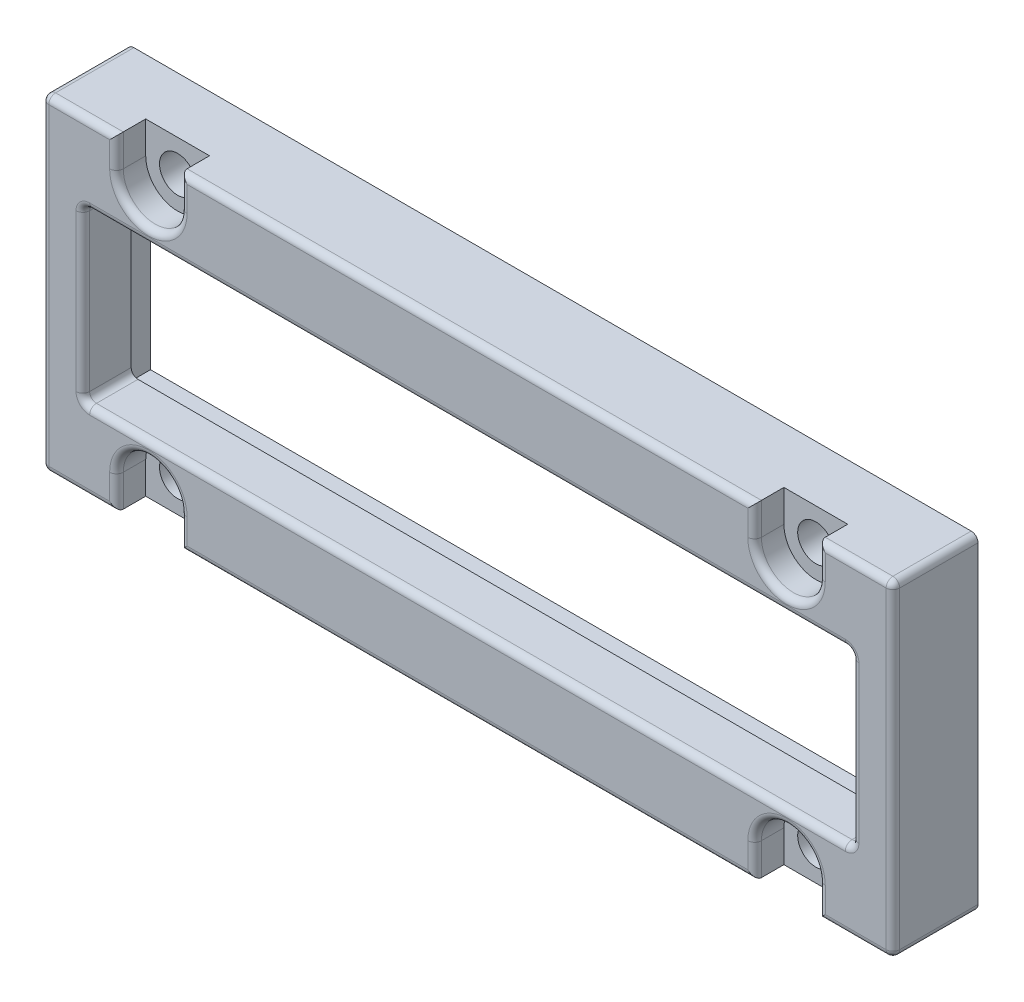
SolidWorks part; units mm, degrees
material "Nylon 101"
ref_plane "Front Plane" through (0, 0, 0) normal (0, 0, 1) x (1, 0, 0)
ref_plane "Top Plane" through (0, 0, 0) normal (0, 1, 0) x (1, 0, 0)
ref_plane "Right Plane" through (0, 0, 0) normal (1, 0, 0) x (0, 0, -1)
sketch "Sketch1" plane through (0, 0, 0) normal (0, 0, 1) x (1, 0, 0)
  line L1 (168.9878, -189.8186) -> (105.4878, -189.8186)
  line L2 (168.9878, -189.8186) -> (168.9878, -165.4346)
  line L3 (168.9878, -165.4346) -> (105.4878, -165.4346)
  line L4 (105.4878, -189.8186) -> (105.4878, -165.4346)
  line L5 (168.9878, -189.8186) -> (105.4878, -165.4346) construction
  line L6 (168.9878, -165.4346) -> (105.4878, -189.8186) construction
  point P4 (137.2378, -177.6266)
extrude "Boss-Extrude1" add sketch "Sketch1" along normal blind 6.35
hole_wizard "CBORE for #2 Socket Head Cap Screw1" positions "Sketch3" profile "Sketch2" counterbore size "#2" standard "ANSI Inch" end condition through all
sketch "Sketch3" plane through (0, 0, 6.35) normal (0, 0, 1) x (1, 0, 0)
  line L0 (163.0823, -187.7866) -> (161.0503, -187.7866) construction
  line L2 (161.0503, -189.8186) -> (161.0503, -165.4346) construction
  line L3 (105.4878, -189.8186) -> (168.9878, -189.8186) construction
  line L4 (168.9878, -165.4346) -> (105.4878, -165.4346) construction
  line L5 (161.0503, -177.6266) -> (168.9878, -177.6266) construction
  line L6 (168.9878, -189.8186) -> (168.9878, -165.4346) construction
  line L8 (137.2378, -189.8186) -> (137.2378, -165.4346) construction
  point P14 (161.0503, -187.431)
  point P26 (113.4253, -187.431)
  point P28 (161.0503, -167.8222)
  point P29 (113.4253, -167.8222)
  dimension "D1" = 2.3876
sketch "Sketch2" plane through (161.0503, -187.431, 6.35) normal (1, 0, 0) x (0, -1, 0)
  line L0 (0, 0) -> (0, 6.35)
  line L1 (0, 6.35) -> (1.3525, 6.35)
  line L3 (1.3525, 6.35) -> (1.3526, 2.1844)
  line L4 (1.3526, 2.1844) -> (2.3812, 2.1844)
  line L5 (2.3812, 2.1844) -> (2.3812, 0)
  line L7 (2.3812, 0) -> (0, 0)
  line L11 (0, -6.35) -> (0, 107.95) construction
  dimension "Thru Hole Dia." = 2.7051
  dimension "Thru Hole Depth" = 6.35
  dimension "C'Bore Dia." = 4.7625
  dimension "C'Bore Depth" = 2.1844
sketch "Sketch4" plane through (0, 0, 6.35) normal (0, 0, 1) x (1, 0, 0)
  line L1 (165.9398, -183.9766) -> (108.5358, -183.9766)
  line L2 (165.9398, -183.9766) -> (165.9398, -171.2766)
  line L3 (165.9398, -171.2766) -> (108.5358, -171.2766)
  line L4 (108.5358, -183.9766) -> (108.5358, -171.2766)
  line L5 (165.9398, -183.9766) -> (108.5358, -171.2766) construction
  line L6 (165.9398, -171.2766) -> (108.5358, -183.9766) construction
  point P4 (137.2378, -177.6266)
extrude "Cut-Extrude1" cut sketch "Sketch4" against normal through all
sketch "Sketch5" plane through (0, 0, 6.35) normal (0, 0, 1) x (1, 0, 0)
  line L0 (168.9878, -165.4346) -> (105.4878, -165.4346) construction
  line L1 (111.0441, -167.8222) -> (115.8066, -167.8222)
  line L2 (111.0441, -167.8222) -> (111.0441, -165.4346)
  line L3 (111.0441, -165.4346) -> (115.8066, -165.4346)
  line L4 (115.8066, -167.8222) -> (115.8066, -165.4346)
  line L5 (111.0441, -167.8222) -> (115.8066, -165.4346) construction
  line L6 (111.0441, -165.4346) -> (115.8066, -167.8222) construction
  line L7 (137.2378, -165.4346) -> (137.2378, -177.6266) construction
  line L8 (137.2378, -177.6266) -> (105.4878, -177.6266) construction
  line L9 (105.4878, -165.4346) -> (105.4878, -189.8186) construction
  line L10 (163.4316, -167.8222) -> (163.4316, -165.4346)
  line L11 (163.4316, -165.4346) -> (158.6691, -165.4346)
  line L12 (158.6691, -167.8222) -> (158.6691, -165.4346)
  line L13 (163.4316, -167.8222) -> (158.6691, -167.8222)
  line L14 (111.0441, -189.8186) -> (115.8066, -189.8186)
  line L15 (111.0441, -187.431) -> (111.0441, -189.8186)
  line L16 (111.0441, -187.431) -> (115.8066, -187.431)
  line L17 (115.8066, -187.431) -> (115.8066, -189.8186)
  line L18 (163.4316, -187.431) -> (158.6691, -187.431)
  line L19 (158.6691, -187.431) -> (158.6691, -189.8186)
  line L20 (163.4316, -189.8186) -> (158.6691, -189.8186)
  line L21 (163.4316, -187.431) -> (163.4316, -189.8186)
  circle A0 centre (113.4253, -167.8222) radius 2.3813 construction
  point P0 (113.4253, -167.8222)
  point P6 (113.4253, -166.6284)
  point P11 (113.4253, -167.8222)
extrude "Cut-Extrude2" cut sketch "Sketch5" against normal up to surface (2.1844 mm away) up to face at (114.7779, -167.8222, 4.1656)
sketch "Sketch7" plane through (0, 0, 0) normal (0, 0, -1) x (-1, 0, 0)
  line L0 (-163.4316, -167.8222) -> (-163.4316, -165.4346) construction
  line L1 (-158.6691, -165.4346) -> (-158.6691, -167.8222) construction
  line L2 (-115.8066, -167.8222) -> (-115.8066, -165.4346) construction
  line L3 (-111.0441, -165.4346) -> (-111.0441, -167.8222) construction
  line L4 (-111.0441, -187.431) -> (-111.0441, -189.8186) construction
  line L5 (-115.8066, -189.8186) -> (-115.8066, -187.431) construction
  line L6 (-158.6691, -187.431) -> (-158.6691, -189.8186) construction
  line L7 (-163.4316, -189.8186) -> (-163.4316, -187.431) construction
  line L8 (-163.4316, -167.8222) -> (-163.4316, -166.7046)
  line L9 (-158.6691, -166.7046) -> (-158.6691, -167.8222)
  line L10 (-115.8066, -167.8222) -> (-115.8066, -166.7046)
  line L11 (-111.0441, -166.7046) -> (-111.0441, -167.8222)
  line L12 (-111.0441, -187.431) -> (-111.0441, -188.5486)
  line L13 (-115.8066, -188.5486) -> (-115.8066, -187.431)
  line L14 (-158.6691, -187.431) -> (-158.6691, -188.5486)
  line L15 (-163.4316, -188.5486) -> (-163.4316, -187.431)
  line L20 (-168.9878, -165.4346) -> (-168.9878, -189.8186)
  line L21 (-168.9878, -189.8186) -> (-105.4878, -189.8186)
  line L22 (-105.4878, -189.8186) -> (-105.4878, -165.4346)
  line L23 (-105.4878, -165.4346) -> (-168.9878, -165.4346)
  line L24 (-168.9878, -165.4346) -> (-168.9878, -189.8186) construction
  line L25 (-168.9878, -189.8186) -> (-105.4878, -189.8186) construction
  line L26 (-105.4878, -189.8186) -> (-105.4878, -165.4346) construction
  line L27 (-105.4878, -165.4346) -> (-168.9878, -165.4346) construction
  line L28 (-106.7578, -166.7046) -> (-111.0441, -166.7046)
  line L29 (-167.7178, -166.7046) -> (-167.7178, -188.5486)
  line L30 (-167.7178, -188.5486) -> (-163.4316, -188.5486)
  line L31 (-106.7578, -188.5486) -> (-106.7578, -166.7046)
  line L32 (-165.9398, -183.9766) -> (-108.5358, -183.9766)
  line L33 (-165.9398, -171.2766) -> (-165.9398, -183.9766)
  line L34 (-108.5358, -171.2766) -> (-165.9398, -171.2766)
  line L35 (-108.5358, -183.9766) -> (-108.5358, -171.2766)
  line L36 (-165.9398, -183.9766) -> (-108.5358, -183.9766)
  line L37 (-165.9398, -171.2766) -> (-165.9398, -183.9766)
  line L38 (-108.5358, -171.2766) -> (-165.9398, -171.2766)
  line L39 (-108.5358, -183.9766) -> (-108.5358, -171.2766)
  line L40 (-163.4316, -166.7046) -> (-167.7178, -166.7046)
  line L41 (-106.7578, -166.7046) -> (-167.7178, -166.7046) construction
  line L42 (-115.8066, -166.7046) -> (-158.6691, -166.7046)
  line L43 (-111.0441, -188.5486) -> (-106.7578, -188.5486)
  line L44 (-167.7178, -188.5486) -> (-106.7578, -188.5486) construction
  line L45 (-158.6691, -188.5486) -> (-115.8066, -188.5486)
  arc A0 (-163.4316, -167.8222) -> (-158.6691, -167.8222) centre (-161.0503, -167.8222) ccw construction
  arc A1 (-115.8066, -167.8222) -> (-111.0441, -167.8222) centre (-113.4253, -167.8222) ccw construction
  arc A2 (-111.0441, -187.431) -> (-115.8066, -187.431) centre (-113.4253, -187.431) ccw construction
  arc A3 (-158.6691, -187.431) -> (-163.4316, -187.431) centre (-161.0503, -187.431) ccw construction
  arc A4 (-163.4316, -167.8222) -> (-158.6691, -167.8222) centre (-161.0503, -167.8222) ccw
  arc A5 (-115.8066, -167.8222) -> (-111.0441, -167.8222) centre (-113.4253, -167.8222) ccw
  arc A6 (-111.0441, -187.431) -> (-115.8066, -187.431) centre (-113.4253, -187.431) ccw
  arc A7 (-158.6691, -187.431) -> (-163.4316, -187.431) centre (-161.0503, -187.431) ccw
  dimension "D1" = 0
  dimension "D2" = 0
  dimension "D3" = 1.27
extrude "Cut-Extrude3" cut sketch "Sketch7" against normal offset from surface (2.7432 mm away) 1.4224 up to face at (162.4029, -187.431, 4.1656)
fillet "Fillet1" radius 0.508 35 edges at (137.2378, -171.2766, 6.35) (108.5358, -177.6266, 6.35) (137.2378, -183.9766, 6.35) (165.9398, -177.6266, 6.35) (137.2378, -189.8186, 6.35) (115.8066, -188.6248, 6.35) (113.4253, -185.0497, 6.35) (111.0441, -188.6248, 6.35) (108.2659, -189.8186, 6.35) (105.4878, -177.6266, 6.35) (108.2659, -165.4346, 6.35) (111.0441, -166.6284, 6.35) (113.4253, -170.2034, 6.35) (115.8066, -166.6284, 6.35) (137.2378, -165.4346, 6.35) (158.6691, -166.6284, 6.35) (161.0503, -170.2034, 6.35) (163.4316, -166.6284, 6.35) (166.2097, -165.4346, 6.35) (168.9878, -177.6266, 6.35) (166.2097, -189.8186, 6.35) (163.4316, -188.6248, 6.35) (161.0503, -185.0497, 6.35) (158.6691, -188.6248, 6.35) (168.9878, -165.4346, 3.175) (105.4878, -165.4346, 3.175) (105.4878, -189.8186, 3.175) (168.9878, -189.8186, 3.175) (165.9398, -171.2766, 4.5466) (165.9398, -183.9766, 4.5466) (108.5358, -183.9766, 4.5466) (108.5358, -171.2766, 4.5466) (115.8066, -166.7046, 1.3716) (111.0441, -166.7046, 1.3716) (106.7578, -166.7046, 1.3716)
sketch "Sketch8" plane through (0, 0, 0) normal (0, 0, -1) x (-1, 0, 0)
  line L0 (-113.4253, -167.8222) -> (-113.4253, -170.7114) construction
  line L5 (-115.625, -169.6954) -> (-111.2256, -169.6954)
  line L6 (-163.25, -169.6954) -> (-158.8506, -169.6954)
  line L7 (-111.2256, -185.5577) -> (-115.625, -185.5577)
  line L8 (-113.4253, -185.5577) -> (-113.4253, -184.5417) construction
  line L9 (-158.8506, -185.5577) -> (-163.25, -185.5577)
  arc A1 (-115.625, -169.6954) -> (-111.2256, -169.6954) centre (-113.4253, -167.8222) ccw
  arc A3 (-163.25, -169.6954) -> (-158.8506, -169.6954) centre (-161.0503, -167.8222) ccw
  arc A6 (-111.2256, -185.5577) -> (-115.625, -185.5577) centre (-113.4253, -187.431) ccw
  arc A7 (-158.8506, -185.5577) -> (-163.25, -185.5577) centre (-161.0503, -187.431) ccw
  dimension "D1" = 1.016
  dimension "D2" = 1.016
extrude "Cut-Extrude4" [suppressed] cut sketch "Sketch8" against normal up to surface (2.7432 mm away)
sketch "Sketch10" plane through (0, 0, 0) normal (0, 0, -1) x (-1, 0, 0)
  line L0 (-137.2378, -171.2766) -> (-137.2378, -183.9766) construction
  line L1 (-165.4318, -171.2766) -> (-109.0438, -171.2766) construction
  line L2 (-109.0438, -183.9766) -> (-165.4318, -183.9766) construction
  line L4 (-167.2378, -185.6266) -> (-107.2378, -185.6266)
  line L5 (-167.2378, -185.6266) -> (-167.2378, -169.6266)
  line L6 (-167.2378, -169.6266) -> (-107.2378, -169.6266)
  line L7 (-107.2378, -185.6266) -> (-107.2378, -169.6266)
  line L8 (-167.2378, -185.6266) -> (-107.2378, -169.6266) construction
  line L9 (-167.2378, -169.6266) -> (-107.2378, -185.6266) construction
  line L25 (-115.8066, -167.8222) -> (-115.8066, -167.2126)
  line L26 (-116.3146, -166.7046) -> (-158.6691, -166.7046)
  line L27 (-158.6691, -166.7046) -> (-158.6691, -167.8222)
  line L28 (-163.4316, -167.8222) -> (-163.4316, -166.7046)
  line L29 (-163.4316, -166.7046) -> (-167.7178, -166.7046)
  line L30 (-167.7178, -166.7046) -> (-167.7178, -188.5486)
  line L31 (-167.7178, -188.5486) -> (-163.4316, -188.5486)
  line L32 (-163.4316, -188.5486) -> (-163.4316, -187.431)
  line L33 (-158.6691, -187.431) -> (-158.6691, -188.5486)
  line L34 (-158.6691, -188.5486) -> (-115.8066, -188.5486)
  line L35 (-115.8066, -188.5486) -> (-115.8066, -187.431)
  line L36 (-111.0441, -187.431) -> (-111.0441, -188.5486)
  line L37 (-111.0441, -188.5486) -> (-106.7578, -188.5486)
  line L38 (-106.7578, -188.5486) -> (-106.7578, -167.2126)
  line L39 (-107.2658, -166.7046) -> (-110.5361, -166.7046)
  line L40 (-111.0441, -167.2126) -> (-111.0441, -167.8222)
  line L41 (-115.8066, -167.8222) -> (-115.8066, -167.2126)
  line L42 (-116.3146, -166.7046) -> (-158.6691, -166.7046)
  line L43 (-158.6691, -166.7046) -> (-158.6691, -167.8222)
  line L44 (-163.4316, -167.8222) -> (-163.4316, -166.7046)
  line L45 (-163.4316, -166.7046) -> (-167.7178, -166.7046)
  line L46 (-167.7178, -166.7046) -> (-167.7178, -188.5486)
  line L47 (-167.7178, -188.5486) -> (-163.4316, -188.5486)
  line L48 (-163.4316, -188.5486) -> (-163.4316, -187.431)
  line L49 (-158.6691, -187.431) -> (-158.6691, -188.5486)
  line L50 (-158.6691, -188.5486) -> (-115.8066, -188.5486)
  line L51 (-115.8066, -188.5486) -> (-115.8066, -187.431)
  line L52 (-111.0441, -187.431) -> (-111.0441, -188.5486)
  line L53 (-111.0441, -188.5486) -> (-106.7578, -188.5486)
  line L54 (-106.7578, -188.5486) -> (-106.7578, -167.2126)
  line L55 (-107.2658, -166.7046) -> (-110.5361, -166.7046)
  line L56 (-111.0441, -167.2126) -> (-111.0441, -167.8222)
  arc A0 (-162.6042, -185.6266) -> (-163.4316, -187.431) centre (-161.0503, -187.431) ccw
  arc A1 (-114.9792, -185.6266) -> (-115.8066, -187.431) centre (-113.4253, -187.431) ccw
  arc A2 (-111.8714, -169.6266) -> (-111.0441, -167.8222) centre (-113.4253, -167.8222) ccw
  arc A3 (-159.4964, -169.6266) -> (-158.6691, -167.8222) centre (-161.0503, -167.8222) ccw
  arc A7 (-115.8066, -167.2126) -> (-116.3146, -166.7046) centre (-116.3146, -167.2126) ccw
  arc A8 (-163.4316, -167.8222) -> (-158.6691, -167.8222) centre (-161.0503, -167.8222) ccw
  arc A9 (-158.6691, -187.431) -> (-163.4316, -187.431) centre (-161.0503, -187.431) ccw
  arc A10 (-111.0441, -187.431) -> (-115.8066, -187.431) centre (-113.4253, -187.431) ccw
  arc A11 (-106.7578, -167.2126) -> (-107.2658, -166.7046) centre (-107.2658, -167.2126) ccw
  arc A12 (-110.5361, -166.7046) -> (-111.0441, -167.2126) centre (-110.5361, -167.2126) ccw
  arc A13 (-115.8066, -167.8222) -> (-111.0441, -167.8222) centre (-113.4253, -167.8222) ccw
  arc A14 (-115.8066, -167.2126) -> (-116.3146, -166.7046) centre (-116.3146, -167.2126) ccw
  arc A15 (-163.4316, -167.8222) -> (-162.6042, -169.6266) centre (-161.0503, -167.8222) ccw
  arc A16 (-158.6691, -187.431) -> (-159.4964, -185.6266) centre (-161.0503, -187.431) ccw
  arc A17 (-111.0441, -187.431) -> (-111.8714, -185.6266) centre (-113.4253, -187.431) ccw
  arc A18 (-106.7578, -167.2126) -> (-107.2658, -166.7046) centre (-107.2658, -167.2126) ccw
  arc A19 (-110.5361, -166.7046) -> (-111.0441, -167.2126) centre (-110.5361, -167.2126) ccw
  arc A20 (-115.8066, -167.8222) -> (-114.9792, -169.6266) centre (-113.4253, -167.8222) ccw
  point P6 (-137.2378, -177.6266)
  line M2 (-167.7178, -166.7046) -> (-163.4316, -166.7046)
  line M3 (-163.4316, -166.7046) -> (-163.4316, -167.8222)
  arc M4 (-163.4316, -167.8222) -> (-158.6691, -167.8222) centre (-161.0503, -167.8222) ccw
  line M5 (-158.6691, -167.8222) -> (-158.6691, -166.7046)
  line M6 (-158.6691, -166.7046) -> (-116.3146, -166.7046)
  arc M7 (-116.3146, -166.7046) -> (-115.8066, -167.2126) centre (-116.3146, -167.2126) cw
  line M8 (-115.8066, -167.2126) -> (-115.8066, -167.8222)
  arc M9 (-115.8066, -167.8222) -> (-111.0441, -167.8222) centre (-113.4253, -167.8222) ccw
  line M10 (-111.0441, -167.8222) -> (-111.0441, -167.2126)
  arc M11 (-111.0441, -167.2126) -> (-110.5361, -166.7046) centre (-110.5361, -167.2126) cw
  line M12 (-110.5361, -166.7046) -> (-107.2658, -166.7046)
  arc M13 (-107.2658, -166.7046) -> (-106.7578, -167.2126) centre (-107.2658, -167.2126) cw
  line M14 (-106.7578, -167.2126) -> (-106.7578, -188.5486)
  line M15 (-106.7578, -188.5486) -> (-111.0441, -188.5486)
  line M16 (-111.0441, -188.5486) -> (-111.0441, -187.431)
  arc M17 (-111.0441, -187.431) -> (-115.8066, -187.431) centre (-113.4253, -187.431) ccw
  line M18 (-115.8066, -187.431) -> (-115.8066, -188.5486)
  line M19 (-115.8066, -188.5486) -> (-158.6691, -188.5486)
  line M20 (-158.6691, -188.5486) -> (-158.6691, -187.431)
  arc M21 (-158.6691, -187.431) -> (-163.4316, -187.431) centre (-161.0503, -187.431) ccw
  line M22 (-163.4316, -187.431) -> (-163.4316, -188.5486)
  line M23 (-163.4316, -188.5486) -> (-167.7178, -188.5486)
  line M24 (-167.7178, -188.5486) -> (-167.7178, -166.7046)
  dimension "D1" = 16
  dimension "D2" = 60
  dimension "D3" = 0
sketch "Sketch11" plane through (0, 0, 2.7432) normal (0, 0, -1) x (-1, 0, 0)
  line L0 (-107.2378, -185.6266) -> (-107.2378, -169.6266) construction
  line L1 (-167.2378, -185.6266) -> (-107.2378, -185.6266) construction
  line L2 (-167.2378, -185.6266) -> (-167.2378, -169.6266) construction
  line L3 (-167.2378, -169.6266) -> (-107.2378, -169.6266) construction
  line L4 (-107.2378, -185.6266) -> (-107.2378, -169.6266)
  line L5 (-167.2378, -185.6266) -> (-107.2378, -185.6266)
  line L6 (-167.2378, -185.6266) -> (-167.2378, -169.6266)
  line L7 (-167.2378, -169.6266) -> (-107.2378, -169.6266)
extrude "Cut-Extrude6" cut sketch "Sketch11" along normal through all
extrude "Boss-Extrude2" add sketch "Sketch10" against normal up to next contours L6 M4 M9 M8 M7 M6 M5 | L7 L4 L6 M17 M16 M15 M14 M13 M12 M11 M10 M9 | L4 M21 M20 M19 M18 M17 | L5 L6 L4 M4 M3 M2 M24 M23 M22 M21
equation "\"D2@Sketch8\"=\"D1@Sketch8\""
